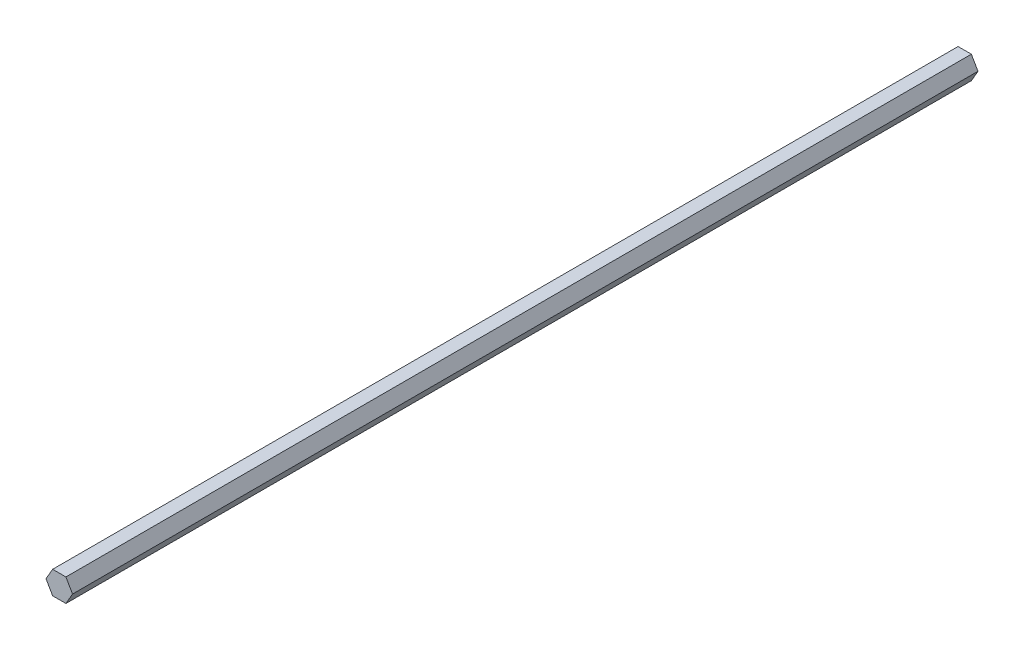
SolidWorks part; units mm, degrees
ref_plane "Front Plane" through (0, 0, 0) normal (0, 0, 1) x (1, 0, 0)
ref_plane "Top Plane" through (0, 0, 0) normal (0, 1, 0) x (1, 0, 0)
ref_plane "Right Plane" through (0, 0, 0) normal (1, 0, 0) x (0, 0, -1)
sketch "Sketch1" plane through (0, 0, 0) normal (0, 0, 1) x (1, 0, 0)
  line L1 (-3.665, 6.348) -> (-7.33, 0)
  line L2 (-7.33, 0) -> (-3.665, -6.348)
  line L3 (-3.665, -6.348) -> (3.665, -6.348)
  line L4 (3.665, -6.348) -> (7.33, 0)
  line L5 (7.33, 0) -> (3.665, 6.348)
  line L6 (3.665, 6.348) -> (-3.665, 6.348)
  circle A0 centre (0, 0) radius 6.348 construction
  point P1 (0, 6.348)
  dimension "D1" = 7.33
extrude "Boss-Extrude1" add sketch "Sketch1" along normal blind 500
